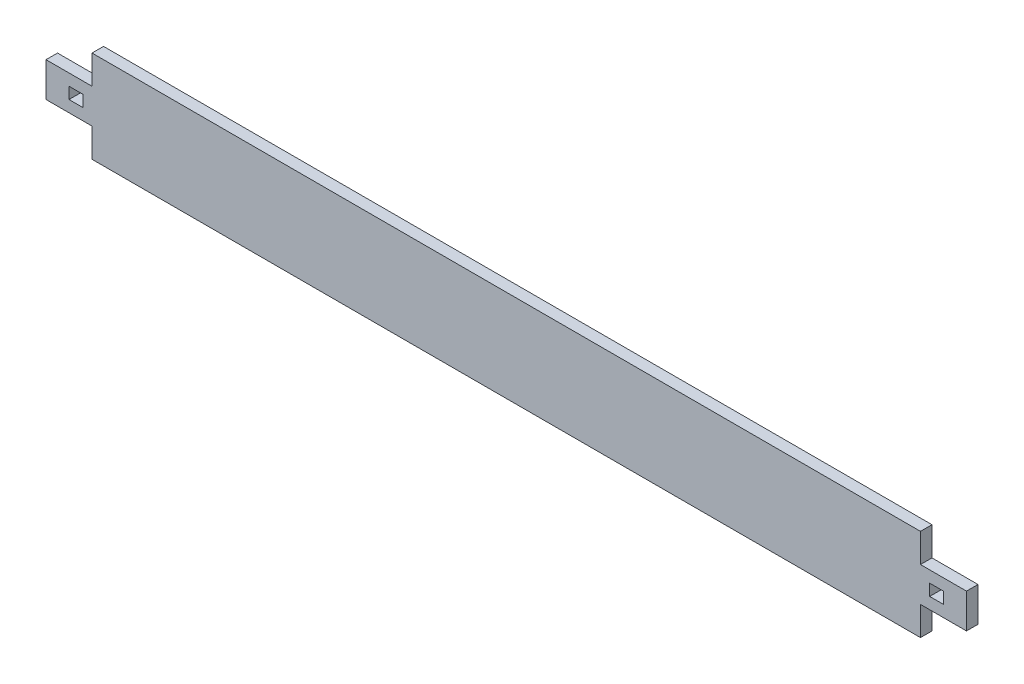
SolidWorks part; units mm, degrees
ref_plane "Front Plane" through (0, 0, 0) normal (0, 0, 1) x (1, 0, 0)
ref_plane "Top Plane" through (0, 0, 0) normal (0, 1, 0) x (1, 0, 0)
ref_plane "Right Plane" through (0, 0, 0) normal (1, 0, 0) x (0, 0, -1)
sketch "Sketch1" plane through (0, 0, 0) normal (0, 0, 1) x (1, 0, 0)
  line L1 (-228.6, -25.4) -> (228.6, -25.4)
  line L2 (-228.6, -25.4) -> (-228.6, 25.4)
  line L3 (-228.6, 25.4) -> (228.6, 25.4)
  line L4 (228.6, -25.4) -> (228.6, 25.4)
  line L5 (-228.6, -25.4) -> (228.6, 25.4) construction
  line L6 (-228.6, 25.4) -> (228.6, -25.4) construction
  point P0 (0, 0)
  dimension "D1" = 457.2
  dimension "D2" = 50.8
extrude "Boss-Extrude1" add sketch "Sketch1" along normal blind 6.35
sketch "Sketch2" plane through (0, 0, 6.35) normal (0, 0, 1) x (1, 0, 0)
  line L0 (-228.6, 25.4) -> (-228.6, -25.4) construction
  line L1 (-254, -9.525) -> (-203.2, -9.525)
  line L2 (-254, -9.525) -> (-254, 9.525)
  line L3 (-254, 9.525) -> (-203.2, 9.525)
  line L4 (-203.2, -9.525) -> (-203.2, 9.525)
  line L5 (-254, -9.525) -> (-203.2, 9.525) construction
  line L6 (-254, 9.525) -> (-203.2, -9.525) construction
  point P0 (-228.6, 0)
  dimension "D1" = 19.05
  dimension "D2" = 25.4
extrude "Boss-Extrude2" add sketch "Sketch2" against normal up to surface (6.35 mm away) up to face at (0, 0, 0)
sketch "Sketch3" plane through (0, 0, 6.35) normal (0, 0, 1) x (1, 0, 0)
  line L0 (-228.6, 25.4) -> (-228.6, 9.525) construction
  line L1 (-241.3, 3.175) -> (-233.68, 3.175)
  line L2 (-241.3, 3.175) -> (-241.3, -3.175)
  line L3 (-241.3, -3.175) -> (-233.68, -3.175)
  line L4 (-233.68, 3.175) -> (-233.68, -3.175)
  line L5 (-233.68, -9.525) -> (-233.68, -3.175) construction
  line L6 (-254, -9.525) -> (-228.6, -9.525) construction
  line L7 (-233.68, 3.175) -> (-233.68, 9.525) construction
  line L8 (-228.6, 9.525) -> (-254, 9.525) construction
  line L9 (-254, 9.525) -> (-254, -9.525) construction
  dimension "D1" = 5.08
  dimension "D2" = 6.35
  dimension "D3" = 12.7
extrude "Cut-Extrude1" cut sketch "Sketch3" against normal through all
mirror "Mirror1" about plane through (0, 0, 0) normal (1, 0, 0) of "Cut-Extrude1", "Boss-Extrude2"
